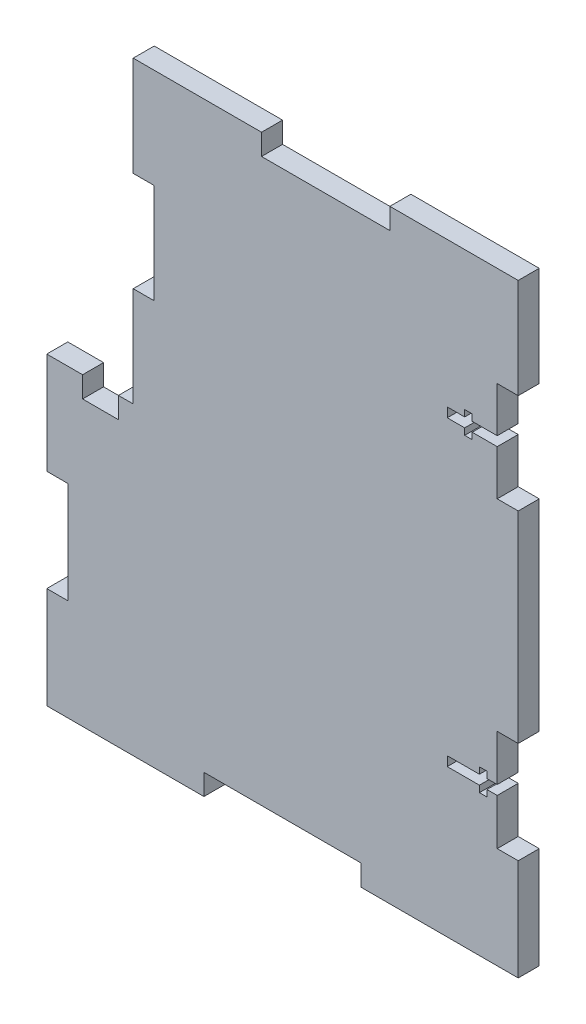
SolidWorks part; units mm, degrees
material "Mahogany"
ref_plane "Front Plane" through (0, 0, 0) normal (0, 0, 1) x (1, 0, 0)
ref_plane "Top Plane" through (0, 0, 0) normal (0, 1, 0) x (1, 0, 0)
ref_plane "Right Plane" through (0, 0, 0) normal (1, 0, 0) x (0, 0, -1)
sketch "Sketch1" plane through (0, 0, 0) normal (0, 0, 1) x (1, 0, 0)
  line L1 (-64.9732, -41.9862) -> (64.9732, -41.9862)
  line L2 (-64.9732, -41.9862) -> (-64.9732, 41.9862)
  line L3 (-64.9732, 41.9862) -> (64.9732, 41.9862)
  line L4 (64.9732, -41.9862) -> (64.9732, 41.9862)
  line L5 (-64.9732, -41.9862) -> (64.9732, 41.9862) construction
  line L6 (-64.9732, 41.9862) -> (64.9732, -41.9862) construction
  point P0 (0, 0)
  dimension "D1" = 129.9464
  dimension "D2" = 83.9724
extrude "Boss-Extrude1" add sketch "Sketch1" along normal blind 5.7912
sketch "Sketch2" plane through (0, 0, 5.7912) normal (0, 0, 1) x (1, 0, 0)
  line L1 (-55.1011, 41.9862) -> (-45.2289, 41.9862)
  line L2 (-55.1011, 41.9862) -> (-55.1011, 36.195)
  line L3 (-55.1011, 36.195) -> (-45.2289, 36.195)
  line L4 (-45.2289, 41.9862) -> (-45.2289, 36.195)
  line L5 (64.9732, 41.9862) -> (-64.9732, 41.9862) construction
  line L6 (0, 0) -> (64.9732, 0) construction
  line L7 (64.9732, -41.9862) -> (64.9732, 41.9862) construction
  dimension "D1" = 9.8721
  dimension "D2" = 5.7912
  dimension "D3" = 9.8721
extrude "Cut-Extrude1" cut sketch "Sketch2" against normal through all
sketch "Sketch3" plane through (0, 0, 5.7912) normal (0, 0, 1) x (1, 0, 0)
  line L0 (-64.9732, 41.9862) -> (-64.9732, -41.9862) construction
  line L1 (-64.9732, 13.9954) -> (-59.182, 13.9954)
  line L2 (-64.9732, 13.9954) -> (-64.9732, -13.9954)
  line L3 (-64.9732, -13.9954) -> (-59.182, -13.9954)
  line L4 (-59.182, 13.9954) -> (-59.182, -13.9954)
  line L5 (0, 0) -> (0, 39.951) construction
  line L6 (64.9732, -13.9954) -> (59.182, -13.9954)
  line L7 (64.9732, 13.9954) -> (64.9732, -13.9954)
  line L8 (64.9732, 13.9954) -> (59.182, 13.9954)
  line L9 (59.182, 13.9954) -> (59.182, -13.9954)
  dimension "D1" = 5.7912
  dimension "D2" = 27.9908
  dimension "D3" = 27.9908
extrude "Cut-Extrude2" cut sketch "Sketch3" against normal through all
sketch "Sketch4" plane through (0, 0, 5.7912) normal (0, 0, 1) x (1, 0, 0)
  line L0 (0, 0) -> (-59.182, 0) construction
  line L1 (-59.182, -13.9954) -> (-59.182, 13.9954) construction
  line L2 (0, 0) -> (0, 28.5152) construction
  line L3 (-59.182, 1.3017) -> (-45.4152, 1.3017) construction
  line L4 (-59.182, 1.3017) -> (-59.182, -1.3018) construction
  line L5 (-59.182, -1.3018) -> (-45.4152, -1.3018) construction
  line L6 (-45.4152, 1.3017) -> (-45.4152, -1.3018) construction
  line L7 (45.4152, 1.3018) -> (45.4152, -1.3018)
  line L8 (59.182, -1.3017) -> (45.4152, -1.3018)
  line L9 (59.182, 1.3017) -> (59.182, -1.3017)
  line L10 (59.182, 1.3017) -> (45.4152, 1.3018)
  line L11 (-64.9732, -13.9954) -> (-64.9732, 13.9954) construction
  point P9 (-45.4152, 0)
  dimension "D1" = 1.3017
  dimension "D2" = 19.558
extrude "Cut-Extrude3" cut sketch "Sketch4" against normal through all
sketch "Sketch6" plane through (0, 0, 5.7912) normal (0, 0, 1) x (1, 0, 0)
  line L0 (-55.3212, 1.3018) -> (-55.3212, -1.3018) construction
  line L11 (0, 0) -> (19.2929, 0) construction
  line L12 (0, 0) -> (0, 14.5303) construction
  line L13 (-55.3212, 1.3018) -> (-62.6683, 1.3018) construction
  line L14 (-62.6683, 1.3018) -> (-62.6683, -1.3018) construction
  line L15 (-62.6683, -1.3018) -> (-55.3212, -1.3018) construction
  line L16 (-54.2798, 0) -> (-55.3212, 0) construction
  line L17 (-55.3212, -1.3018) -> (-55.3212, -3.0861) construction
  line L18 (-56.3626, 3.0861) -> (-54.2798, 3.0861) construction
  line L19 (-56.3626, 3.0861) -> (-56.3626, -3.0861) construction
  line L20 (-56.3626, -3.0861) -> (-54.2798, -3.0861) construction
  line L21 (-54.2798, 3.0861) -> (-54.2798, -3.0861) construction
  line L24 (-48.5394, 0) -> (-54.2798, 0) construction
  line L26 (56.3626, -3.0861) -> (54.2798, -3.0861)
  line L27 (54.2798, 3.0861) -> (54.2798, -3.0861)
  line L28 (56.3626, 3.0861) -> (56.3626, -3.0861)
  line L29 (56.3626, 3.0861) -> (54.2798, 3.0861)
  dimension "D3" = 2.0828
  dimension "D4" = 6.1722
  dimension "D5" = 2.6035
extrude "Cut-Extrude5" cut sketch "Sketch6" against normal through all
sketch "Sketch7" plane through (0, 0, 5.7912) normal (0, 0, 1) x (1, 0, 0)
  line L0 (64.9732, 41.9862) -> (64.9732, 124.5362)
  line L1 (64.9732, 124.5362) -> (-41.148, 124.5362)
  line L2 (-41.148, 124.5362) -> (-41.148, 41.9862)
  line L3 (64.9732, 41.9862) -> (-45.2289, 41.9862) construction
  line L72 (59.182, -1.3018) -> (56.3626, -1.3017)
  line L73 (56.3626, -1.3017) -> (56.3626, -3.0861)
  line L74 (56.3626, -3.0861) -> (54.2798, -3.0861)
  line L75 (54.2798, -3.0861) -> (54.2798, -1.3017)
  line L76 (54.2798, -1.3017) -> (45.4152, -1.3017)
  line L77 (45.4152, -1.3017) -> (45.4152, 1.3018)
  line L78 (45.4152, 1.3018) -> (54.2798, 1.3018)
  line L79 (54.2798, 1.3018) -> (54.2798, 3.0861)
  line L80 (54.2798, 3.0861) -> (56.3626, 3.0861)
  line L81 (56.3626, 3.0861) -> (56.3626, 1.3018)
  line L82 (56.3626, 1.3018) -> (59.182, 1.3018)
  line L83 (59.182, 1.3018) -> (59.182, 13.9954)
  line L84 (59.182, 13.9954) -> (64.9732, 13.9954)
  line L85 (64.9732, 13.9954) -> (64.9732, 41.9862)
  line L86 (64.9732, 41.9862) -> (-45.2289, 41.9862)
  line L87 (-45.2289, 41.9862) -> (-45.2289, 36.195)
  line L88 (-45.2289, 36.195) -> (-55.1011, 36.195)
  line L101 (-55.1011, 36.195) -> (-55.1011, 41.9862)
  line L102 (-55.1011, 41.9862) -> (-64.9732, 41.9862)
  line L103 (-64.9732, 41.9862) -> (-64.9732, 13.9954)
  line L104 (-64.9732, 13.9954) -> (-59.182, 13.9954)
  line L105 (-59.182, 13.9954) -> (-59.182, -13.9954)
  line L118 (-59.182, -13.9954) -> (-64.9732, -13.9954)
  line L119 (-64.9732, -13.9954) -> (-64.9732, -41.9862)
  line L120 (-64.9732, -41.9862) -> (64.9732, -41.9862)
  line L137 (64.9732, -41.9862) -> (64.9732, -13.9954)
  line L138 (64.9732, -13.9954) -> (59.182, -13.9954)
  line L139 (59.182, -13.9954) -> (59.182, -1.3018)
  line L154 (64.9732, 41.9862) -> (-41.148, 41.9862)
  dimension "D1" = 82.55
  dimension "D2" = 106.1212
  dimension "D3" = 0
extrude "Boss-Extrude2" add sketch "Sketch7" against normal blind 5.7912
sketch "Sketch8" plane through (0, 0, 5.7912) normal (0, 0, 1) x (1, 0, 0)
  line L0 (-64.9732, -41.9862) -> (64.9732, -41.9862) construction
  line L1 (21.6577, -41.9862) -> (-21.6577, -41.9862)
  line L2 (21.6577, -41.9862) -> (21.6577, -36.195)
  line L3 (21.6577, -36.195) -> (-21.6577, -36.195)
  line L4 (-21.6577, -41.9862) -> (-21.6577, -36.195)
  dimension "D1" = 5.7912
  dimension "D2" = 43.3155
  dimension "D3" = 43.3155
extrude "Cut-Extrude6" cut sketch "Sketch8" against normal through all
sketch "Sketch12" plane through (0, 0, 5.7912) normal (0, 0, 1) x (1, 0, 0)
  line L0 (64.9732, 13.9954) -> (64.9732, 124.5362) construction
  line L1 (64.9732, 69.5029) -> (59.182, 69.5029)
  line L2 (64.9732, 69.5029) -> (64.9732, 97.0195)
  line L3 (64.9732, 97.0195) -> (59.182, 97.0195)
  line L4 (59.182, 69.5029) -> (59.182, 97.0195)
  line L5 (11.9126, 124.5362) -> (11.9126, 42.6911) construction
  line L6 (64.9732, 124.5362) -> (-41.148, 124.5362) construction
  line L7 (-35.3568, 69.5029) -> (-35.3568, 97.0195)
  line L8 (-41.148, 97.0195) -> (-35.3568, 97.0195)
  line L9 (-41.148, 69.5029) -> (-41.148, 97.0195)
  line L10 (-41.148, 69.5029) -> (-35.3568, 69.5029)
  dimension "D1" = 5.7912
  dimension "D2" = 27.5167
  dimension "D3" = 27.5167
extrude "Cut-Extrude9" cut sketch "Sketch12" against normal through all
sketch "Sketch13" plane through (0, 0, 5.7912) normal (0, 0, 1) x (1, 0, 0)
  line L0 (45.4152, 83.2612) -> (59.182, 83.2612) construction
  line L1 (59.182, 97.0195) -> (59.182, 69.5029) construction
  line L5 (45.4152, 81.9595) -> (59.182, 81.9595)
  line L6 (45.4152, 81.9595) -> (45.4152, 84.563)
  line L7 (45.4152, 84.563) -> (59.182, 84.563)
  line L8 (59.182, 81.9595) -> (59.182, 84.563)
  dimension "D1" = 2.6035
  dimension "D2" = 13.7668
extrude "Cut-Extrude10" cut sketch "Sketch13" against normal through all
sketch "Sketch14" plane through (0, 0, 5.7912) normal (0, 0, 1) x (1, 0, 0)
  line L0 (52.2986, 93.7894) -> (59.182, 93.7894) construction
  line L1 (52.2986, 80.1751) -> (50.2158, 80.1751)
  line L2 (52.2986, 80.1751) -> (52.2986, 86.3473)
  line L3 (52.2986, 86.3473) -> (50.2158, 86.3473)
  line L4 (50.2158, 80.1751) -> (50.2158, 86.3473)
  line L5 (59.182, 97.0195) -> (59.182, 84.563) construction
  line L6 (59.182, 84.563) -> (45.4152, 84.563) construction
  line L7 (12.0142, 120.2944) -> (12.0142, -38.735) construction
  point P8 (50.2158, 84.563)
  dimension "D1" = 2.0828
  dimension "D2" = 6.1722
  dimension "D3" = 6.8834
  dimension "D4" = 1.7844
extrude "Cut-Extrude11" cut sketch "Sketch14" against normal through all
sketch "Sketch15" plane through (0, 0, 5.7912) normal (0, 0, 1) x (1, 0, 0)
  line L0 (64.9732, 124.5362) -> (-41.148, 124.5362) construction
  line L1 (29.5995, 124.5362) -> (-5.7743, 124.5362)
  line L2 (29.5995, 124.5362) -> (29.5995, 118.745)
  line L3 (29.5995, 118.745) -> (-5.7743, 118.745)
  line L4 (-5.7743, 124.5362) -> (-5.7743, 118.745)
  dimension "D1" = 5.7912
  dimension "D2" = 35.3737
  dimension "D3" = 35.3737
extrude "Cut-Extrude12" cut sketch "Sketch15" against normal through all
equation "\"Length\"= \"Length@Box.SLDASM\""
equation "\"D1@Sketch1\"  = \"Length\" + 2 * \"Material\""
equation "\"Width\"= \"Short Height@Box.SLDASM\""
equation "\"D2@Sketch1\" = \"Width\" + 2 * \"Material\""
equation "\"Material\"= \"Material@Box.SLDASM\""
equation "\"D1@Boss-Extrude1\" = \"Material\""
equation "\"D1@Sketch2\"=(\"Length\" -\"Over Hang@Box.SLDASM\"+\"Material\"*2)/3"
equation "\"D2@Sketch2\"= \"Material\""
equation "\"D3@Sketch2\"=(\"Length\" -\"Over Hang@Box.SLDASM\"+\"Material\"*2)/3"
equation "\"D1@Sketch3\"=\"Material\""
equation "\"D2@Sketch3\"=(\"Width\" +\"Material\"*2)/3"
equation "\"D3@Sketch3\"=(\"Width\" +\"Material\"*2)/3"
equation "\"Diameter of Screw\"= \"Diameter of Screw@Box.SLDASM\""
equation "\"Length of screw\"= \"Length of Screw@Box.SLDASM\""
equation "\"D1@Sketch4\"= \"Diameter of Screw\" /2"
equation "\"D2@Sketch4\"=\"Length of screw\""
equation "\"Diameter of Nut\"= \"Diameter of Nut@Box.SLDASM\""
equation "\"Height of Nut\"= \"Height of Nut@Box.SLDASM\""
equation "\"D3@Sketch6\"= \"Height of Nut\""
equation "\"D4@Sketch6\"=\"Diameter of Nut\""
equation "\"D1@Sketch7\"= \"Long Height@Box.SLDASM\"-\"Short Height@Box.SLDASM\""
equation "\"D2@Sketch7\" = \"Over Hang@Box.SLDASM\" + \"Material\""
equation "\"D1@Boss-Extrude2\" = \"Material\""
equation "\"D1@Sketch8\"= \"Material\""
equation "\"D2@Sketch8\"=(\"Length\" + \"Material\"*2)/3"
equation "\"D3@Sketch8\"=(\"Length\" + \"Material\"*2)/3"
equation "\"D1@Sketch12\"=\"Material\""
equation "\"D2@Sketch12\"=(\"Long Height@Box.SLDASM\"-\"Short Height@Box.SLDASM\")/3"
equation "\"D3@Sketch12\"=(\"Long Height@Box.SLDASM\"-\"Short Height@Box.SLDASM\")/3"
equation "\"D1@Sketch13\"=\"Diameter of Screw\""
equation "\"D2@Sketch13\"=\"Length of screw\"-\"Material\""
equation "\"D1@Sketch14\"=\"Height of Nut\""
equation "\"D2@Sketch14\"=\"Diameter of Nut\""
equation "\"D3@Sketch14\"=(\"Length of screw\"-\"Material\")/2"
equation "\"D4@Sketch14\"=(\"Diameter of Nut\"-\"Diameter of Screw\")/2"
equation "\"D1@Sketch15\"= \"Material\""
equation "\"D2@Sketch15\"=(\"Material\"+ \"over hang@Box.SLDASM\" )/3"
equation "\"D3@Sketch15\"=(\"Material\" + \"over hang@Box.SLDASM\" )/3"
equation "\"D5@Sketch6\"=\"Diameter of Screw\""
